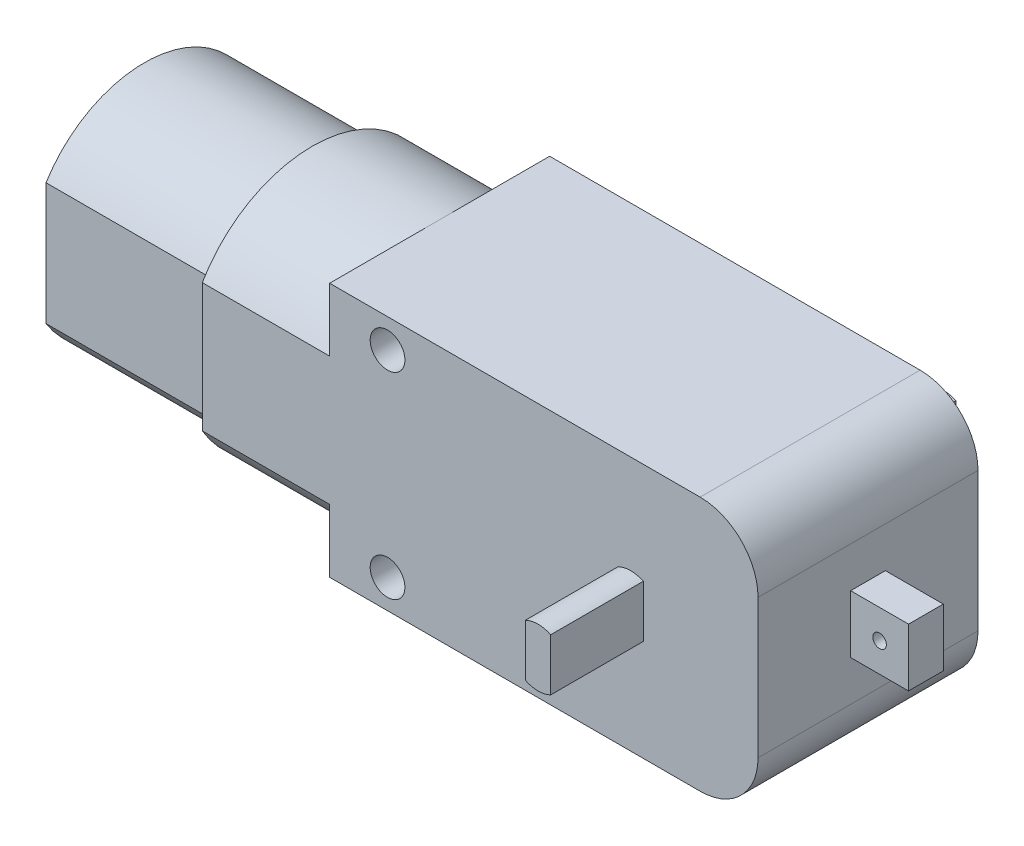
SolidWorks part; units mm, degrees
ref_plane "Front Plane" through (0, 0, 0) normal (0, 0, 1) x (1, 0, 0)
ref_plane "Top Plane" through (0, 0, 0) normal (0, 1, 0) x (1, 0, 0)
ref_plane "Right Plane" through (0, 0, 0) normal (1, 0, 0) x (0, 0, -1)
sketch "Sketch1" plane through (0, 0, 0) normal (0, 0, 1) x (1, 0, 0)
  line L0 (-37.4341, 0) -> (37.4341, 0) construction
  line L1 (-18.5, -11) -> (13.5, -11)
  line L2 (-18.5, -11) -> (-18.5, 11)
  line L3 (-18.5, 11) -> (13.5, 11)
  line L4 (18.5, -6) -> (18.5, 6)
  line L5 (0, -21.4508) -> (0, 21.4508) construction
  arc A0 (18.5, 6) -> (13.5, 11) centre (13.5, 6) ccw
  arc A1 (13.5, -11) -> (18.5, -6) centre (13.5, -6) ccw
  circle A2 centre (-13.5, 8.5) radius 1.5
  circle A3 centre (-13.5, -8.5) radius 1.5
  point P0 (0, 0)
  point P14 (0, 0)
  point P16 (0, 0)
  dimension "D3" = 10
  dimension "D2" = 10
  dimension "D7" = 3
  dimension "D1" = 37
  dimension "D4" = 22
  dimension "D5" = 18.5
  dimension "D6" = 11
  dimension "D8" = 2.5
  dimension "D9" = 5
extrude "Boss-Extrude1" add sketch "Sketch1" along normal blind 19
sketch "Sketch2" plane through (18.5, 0, 0) normal (1, 0, 0) x (0, 0, -1)
  line L1 (-11, 2.5) -> (-8, 2.5)
  line L2 (-11, 2.5) -> (-11, -2.5)
  line L3 (-11, -2.5) -> (-8, -2.5)
  line L4 (0, -6) -> (0, 6)
  line L5 (0, 6) -> (-19, 6)
  line L6 (-19, 6) -> (-19, -6)
  line L7 (-19, -6) -> (0, -6)
  line L8 (0, -6) -> (0, 6)
  line L9 (0, 6) -> (-19, 6)
  line L10 (-19, 6) -> (-19, -6)
  line L11 (-19, -6) -> (0, -6)
  line L12 (-8, 2.5) -> (-8, -2.5)
  line L13 (-11, 2.5) -> (-8, -2.5) construction
  line L14 (-11, -2.5) -> (-8, 2.5) construction
  point P2 (-9.5, 0)
  dimension "D2" = 6
  dimension "D3" = 9.5
  dimension "D4" = 5
  dimension "D5" = 3
  dimension "D1" = 0
extrude "Boss-Extrude2" add sketch "Sketch2" along normal blind 5 contours L12 L1 L2 L3
sketch "Sketch3" plane through (0, 0, 11) normal (0, 0, 1) x (1, 0, 0)
  line L4 (18.5, 2.5) -> (18.5, -2.5)
  line L5 (18.5, -2.5) -> (23.5, -2.5)
  line L6 (23.5, -2.5) -> (23.5, 2.5)
  line L7 (23.5, 2.5) -> (18.5, 2.5)
  line L8 (18.5, 2.5) -> (18.5, -2.5)
  line L9 (18.5, -2.5) -> (23.5, -2.5)
  line L10 (23.5, -2.5) -> (23.5, 2.5)
  line L11 (23.5, 2.5) -> (18.5, 2.5)
  circle A0 centre (21, 0) radius 0.5844
  dimension "D3" = 2.5
  dimension "D2" = 2.5
  dimension "D1" = 0
extrude "Cut-Extrude1" cut sketch "Sketch3" against normal blind 5 contours A0
sketch "Sketch4" plane through (0, 0, 19) normal (0, 0, 1) x (1, 0, 0)
  line L0 (8.5897, 2.25) -> (8.5897, -2.25)
  line L1 (6.4103, 2.25) -> (6.4103, -2.25)
  line L4 (18.5, -6) -> (18.5, 6)
  line L5 (13.5, 11) -> (-18.5, 11)
  line L6 (-18.5, 11) -> (-18.5, -11)
  line L7 (-18.5, -11) -> (13.5, -11)
  line L8 (18.5, -6) -> (18.5, 6)
  line L9 (13.5, 11) -> (-18.5, 11)
  line L10 (-18.5, 11) -> (-18.5, -11)
  line L11 (-18.5, -11) -> (13.5, -11)
  arc A0 (8.5897, 2.25) -> (6.4103, 2.25) centre (7.5, 0) ccw
  arc A1 (6.4103, -2.25) -> (8.5897, -2.25) centre (7.5, 0) ccw
  arc A2 (13.5, -11) -> (18.5, -6) centre (13.5, -6) ccw
  arc A3 (18.5, 6) -> (13.5, 11) centre (13.5, 6) ccw
  arc A4 (13.5, -11) -> (18.5, -6) centre (13.5, -6) ccw
  arc A5 (18.5, 6) -> (13.5, 11) centre (13.5, 6) ccw
  point P13 (7.694, 0)
  dimension "D3" = 11
  dimension "D4" = 5
  dimension "D2" = 11
  dimension "D5" = 4.5
  dimension "D6" = 4.5
  dimension "D1" = 0
extrude "Boss-Extrude3" add sketch "Sketch4" along normal blind 8 and the other way blind 27 contours A0
sketch "Sketch5" plane through (-18.5, 0, 0) normal (-1, 0, 0) x (0, 0, 1)
  line L4 (0, 11) -> (0, -11)
  line L5 (0, -11) -> (19, -11)
  line L6 (19, -11) -> (19, 11)
  line L7 (19, 11) -> (0, 11)
  line L8 (0, 11) -> (0, -11)
  line L9 (0, -11) -> (19, -11)
  line L10 (19, -11) -> (19, 11)
  line L11 (19, 11) -> (0, 11)
  arc A0 (0, -5.5453) -> (19, -5.5453) centre (9.5, 0) ccw
  arc A1 (19, 5.5453) -> (0, 5.5453) centre (9.5, 0) ccw
  point P6 (9.5, 11)
  dimension "D2" = 0
  dimension "D1" = 0
extrude "Boss-Extrude4" add sketch "Sketch5" along normal blind 11 contours L10 A1 L8 A0
sketch "Sketch6" plane through (-29.5, 0, 0) normal (-1, 0, 0) x (0, 0, 1)
  line L0 (1, 5.2678) -> (1, -5.2678)
  line L1 (18, -5.2678) -> (18, 5.2678)
  line L2 (19, -5.5453) -> (19, 5.5453)
  line L3 (0, 5.5453) -> (0, -5.5453)
  line L4 (19, -5.5453) -> (19, 5.5453)
  line L5 (0, 5.5453) -> (0, -5.5453)
  arc A0 (18, 5.2678) -> (1, 5.2678) centre (9.5, 0) ccw
  arc A1 (1, -5.2678) -> (18, -5.2678) centre (9.5, 0) ccw
  arc A2 (19, 5.5453) -> (0, 5.5453) centre (9.5, 0) ccw
  arc A3 (0, -5.5453) -> (19, -5.5453) centre (9.5, 0) ccw
  arc A4 (19, 5.5453) -> (0, 5.5453) centre (9.5, 0) ccw
  arc A5 (0, -5.5453) -> (19, -5.5453) centre (9.5, 0) ccw
  dimension "D1" = 0
  dimension "D2" = 1
extrude "Boss-Extrude5" add sketch "Sketch6" along normal blind 8.5 contours A0 L0 A1 L1
sketch "Sketch7" plane through (-38, 0, 0) normal (-1, 0, 0) x (0, 0, 1)
  line L2 (18, -5.2678) -> (18, 5.2678)
  line L3 (1, 5.2678) -> (1, -5.2678)
  line L4 (18, -5.2678) -> (18, 5.2678)
  line L5 (1, 5.2678) -> (1, -5.2678)
  arc A2 (18, 5.2678) -> (1, 5.2678) centre (9.5, 0) ccw
  arc A3 (1, -5.2678) -> (18, -5.2678) centre (9.5, 0) ccw
  arc A4 (18, 5.2678) -> (1, 5.2678) centre (9.5, 0) ccw
  arc A5 (1, -5.2678) -> (18, -5.2678) centre (9.5, 0) ccw
  line M5 (18, -5.2678) -> (18, 5.2678)
  arc M6 (18, 5.2678) -> (1, 5.2678) centre (9.5, 0) ccw
  line M7 (1, 5.2678) -> (1, -5.2678)
  arc M8 (1, -5.2678) -> (18, -5.2678) centre (9.5, 0) ccw
  dimension "D1" = 0
extrude "Boss-Extrude6" add sketch "Sketch7" along normal blind 6 contours M8 M5 M6 M7
